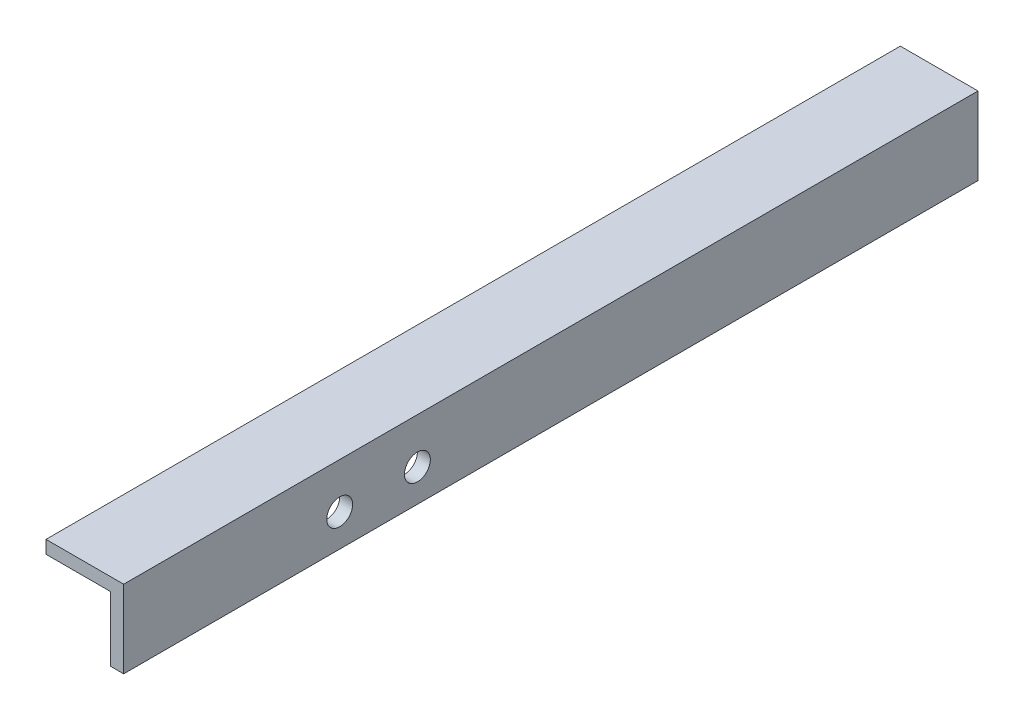
SolidWorks part; units mm, degrees
ref_plane "Front Plane" through (0, 0, 0) normal (0, 0, 1) x (1, 0, 0)
ref_plane "Top Plane" through (0, 0, 0) normal (0, 1, 0) x (1, 0, 0)
ref_plane "Right Plane" through (0, 0, 0) normal (1, 0, 0) x (0, 0, -1)
sketch "Sketch1" plane through (0, 0, 0) normal (0, 0, 1) x (1, 0, 0)
  line L0 (-269.875, 946.3) -> (-269.875, 984.4)
  line L3 (-269.875, 984.4) -> (-307.975, 984.4)
  line L5 (-261.4422, 984.4) -> (-269.875, 984.4) construction
  dimension "D1" = 38.1
extrude "Extrude-Thin1" add sketch "Sketch1" along normal up to surface (215.9 mm away) and the other way up to surface (203.2 mm away) thin thin type one direction reverse wall 6.35
sketch "Sketch2" plane through (-276.225, 0, 0) normal (-1, 0, 0) x (0, 0, 1)
  circle A0 centre (109.9089, 962.175) radius 6.35
  circle A1 centre (71.8089, 962.175) radius 6.35
  dimension "D1" = 12.7
extrude "Cut-Extrude1" cut sketch "Sketch2" against normal through all
